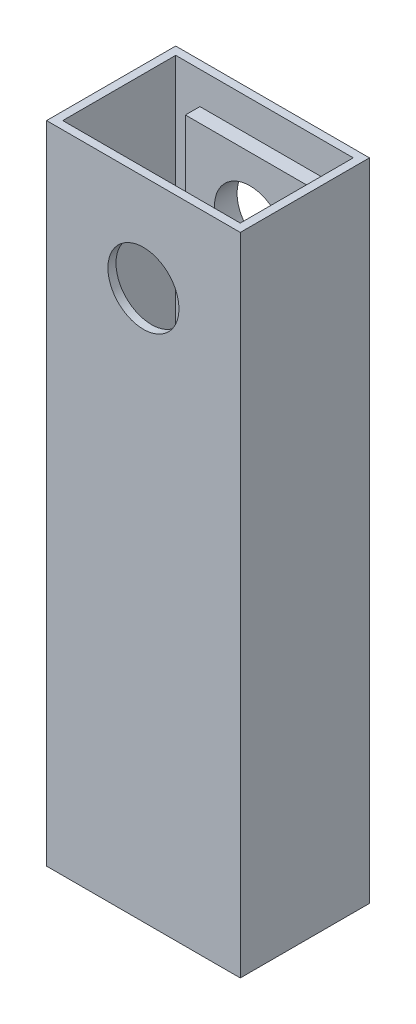
SolidWorks part; units mm, degrees
ref_plane "Front Plane" through (0, 0, 0) normal (0, 0, 1) x (1, 0, 0)
ref_plane "Top Plane" through (0, 0, 0) normal (0, 1, 0) x (1, 0, 0)
ref_plane "Right Plane" through (0, 0, 0) normal (1, 0, 0) x (0, 0, -1)
sketch "Sketch1" plane through (0, 0, 0) normal (0, 1, 0) x (1, 0, 0)
  line L0 (-2.5, -2.5) -> (-57.5, -2.5)
  line L1 (0, 0) -> (-60, 0)
  line L2 (0, 0) -> (0, -40)
  line L3 (0, -40) -> (-60, -40)
  line L4 (-60, 0) -> (-60, -40)
  line L5 (-57.5, -2.5) -> (-57.5, -37.5)
  line L6 (-2.5, -37.5) -> (-57.5, -37.5)
  line L7 (-2.5, -2.5) -> (-2.5, -37.5)
  dimension "D1" = 40
  dimension "D2" = 60
  dimension "D3" = 2.5
extrude "Boss-Extrude1" add sketch "Sketch1" along normal blind 200
sketch "Sketch2" plane through (0, 0, 0) normal (0, 0, -1) x (-1, 0, 0)
  line L0 (0, 200) -> (0, 0) construction
  line L1 (60, 200) -> (0, 200)
  line L2 (60, 200) -> (60, 140)
  line L3 (60, 140) -> (0, 140)
  line L4 (0, 200) -> (0, 140)
  line L5 (0, 200) -> (60, 140)
  circle A0 centre (30, 170) radius 11
  dimension "D2" = 22
  dimension "D1" = 60
extrude "Cut-Extrude1" cut sketch "Sketch2" against normal blind 200 contours L5 A0 | L5 A0
sketch "Sketch3" plane through (0, 0, 2.5) normal (0, 0, 1) x (1, 0, 0)
  line L1 (-10, 150) -> (-50, 150)
  line L2 (-10, 150) -> (-10, 190)
  line L3 (-10, 190) -> (-50, 190)
  line L4 (-50, 150) -> (-50, 190)
  line L5 (-10, 150) -> (-50, 190) construction
  line L6 (-10, 190) -> (-50, 150) construction
  circle A0 centre (-30, 170) radius 11 construction
  circle A1 centre (-30, 170) radius 11
  point P0 (-30, 170)
  dimension "D1" = 40
  dimension "D2" = 40
extrude "Boss-Extrude2" add sketch "Sketch3" along normal blind 4.5
